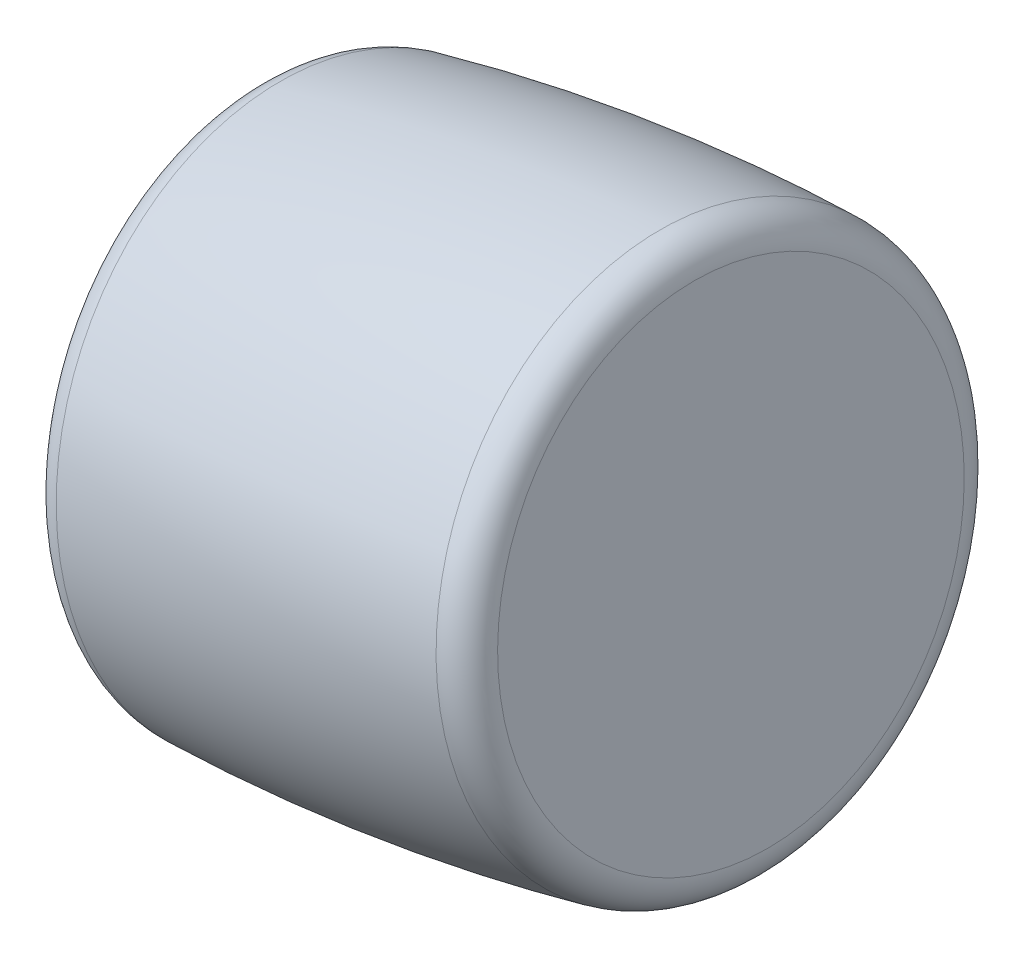
SolidWorks part; units mm, degrees
ref_plane "Front Plane" through (0, 0, 0) normal (0, 0, 1) x (1, 0, 0)
ref_plane "Top Plane" through (0, 0, 0) normal (0, 1, 0) x (1, 0, 0)
ref_plane "Right Plane" through (0, 0, 0) normal (1, 0, 0) x (0, 0, -1)
ref_plane "Plane1" through (0, 0, 0) normal (0, 0, 1) x (1, 0, 0)
sketch "Sketch1" plane through (0, 0, 0) normal (0, 0, 1) x (1, 0, 0)
  line L0 (1.9158, 42.3956) -> (1.0633, 47.6783)
  line L1 (11.2318, 49.3192) -> (12.0842, 44.0364)
  line L2 (12.0842, 44.0364) -> (1.9158, 42.3956)
  line L3 (12.0842, 44.0364) -> (1.9158, 42.3956) construction
  arc A0 (1.0633, 47.6783) -> (1.6179, 48.5244) centre (1.8037, 47.7978) cw
  arc A1 (1.6179, 48.5244) -> (10.4392, 49.9479) centre (13.8846, 0.5519) cw
  arc A2 (10.4392, 49.9479) -> (11.2318, 49.3192) centre (10.4913, 49.1997) cw
revolve "Revolve1" add sketch "Sketch1" angle 360 about L3
